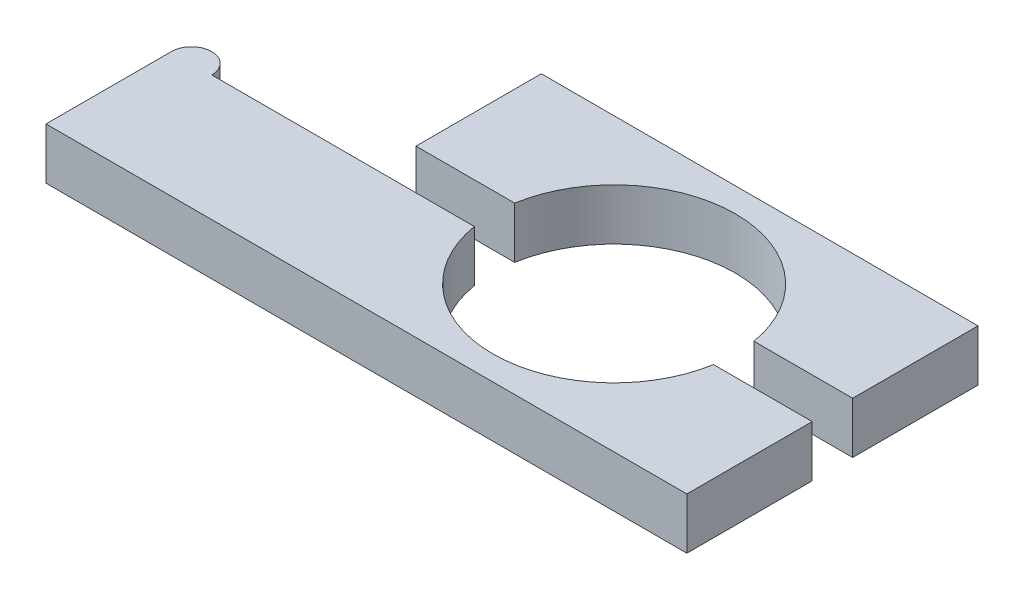
SolidWorks part; units mm, degrees
ref_plane "Front Plane" through (0, 0, 0) normal (0, 0, 1) x (1, 0, 0)
ref_plane "Top Plane" through (0, 0, 0) normal (0, 1, 0) x (1, 0, 0)
ref_plane "Right Plane" through (0, 0, 0) normal (1, 0, 0) x (0, 0, -1)
sketch "Sketch1" plane through (0, 43.1133, 0) normal (0, 1, 0) x (1, 0, 0)
  line L0 (-137.0554, 67.8474) -> (21.4446, 67.8474)
  line L1 (21.4446, 67.8474) -> (21.4446, -4.1526)
  line L2 (21.4446, -4.1526) -> (-137.0554, -4.1526)
  line L3 (-137.0554, -4.1526) -> (-137.0554, 67.8474)
  circle A0 centre (-32.5554, 31.8474) radius 36 construction
  dimension "D1" = 72
  dimension "D2" = 54
  dimension "D3" = 104.5
extrude "Boss-Extrude1" add sketch "Sketch1" against normal blind 12.7
sketch "Sketch2" plane through (0, 43.1133, 0) normal (0, 1, 0) x (1, 0, 0)
  circle A0 centre (-32.5554, 31.8474) radius 30
  dimension "D1" = 60
extrude "Cut-Extrude1" cut sketch "Sketch2" against normal through all
sketch "Sketch3" plane through (0, 43.1133, 0) normal (0, 1, 0) x (1, 0, 0)
  line L0 (-137.0554, 36.8474) -> (21.4446, 36.8474)
  line L1 (-137.0554, 67.8474) -> (-137.0554, -4.1526) construction
  line L2 (21.4446, -4.1526) -> (21.4446, 67.8474) construction
  line L3 (-137.0554, 26.8474) -> (21.4446, 26.8474)
  line L4 (21.4446, 31.8474) -> (-137.0554, 31.8474) construction
  line L5 (-137.0554, 36.8474) -> (-137.0554, 26.8474)
  line L6 (21.4446, 26.8474) -> (21.4446, 36.8474)
  dimension "D1" = 5
extrude "Cut-Extrude3" cut sketch "Sketch3" against normal through all
sketch "Sketch4" plane through (0, 30.4133, 0) normal (0, -1, 0) x (1, 0, 0)
  line L0 (-86.5554, -36.8474) -> (-86.5554, -67.8474)
  line L1 (-62.1358, -36.8474) -> (-137.0554, -36.8474) construction
  line L2 (21.4446, -67.8474) -> (-137.0554, -67.8474) construction
  line L3 (-86.5554, -67.8474) -> (-137.0554, -67.8474)
  line L4 (-137.0554, -67.8474) -> (-137.0554, -36.8474)
  line L5 (-137.0554, -36.8474) -> (-86.5554, -36.8474)
  dimension "D1" = 54
extrude "Cut-Extrude4" cut sketch "Sketch4" against normal through all
sketch "Sketch5" plane through (0, 30.4133, 0) normal (0, -1, 0) x (1, 0, 0)
  line L0 (-137.0554, -26.8474) -> (-62.1358, -26.8474) construction
  line L1 (-137.0554, -26.8474) -> (-127.0554, -26.8474)
  arc A0 (-137.0554, -26.8474) -> (-127.0554, -26.8474) centre (-132.0554, -26.8474) ccw
  dimension "D1" = 5
extrude "Boss-Extrude2" add sketch "Sketch5" against normal up to surface (12.7 mm away) up to face at (-49.3887, 43.1133, -12.3474)
